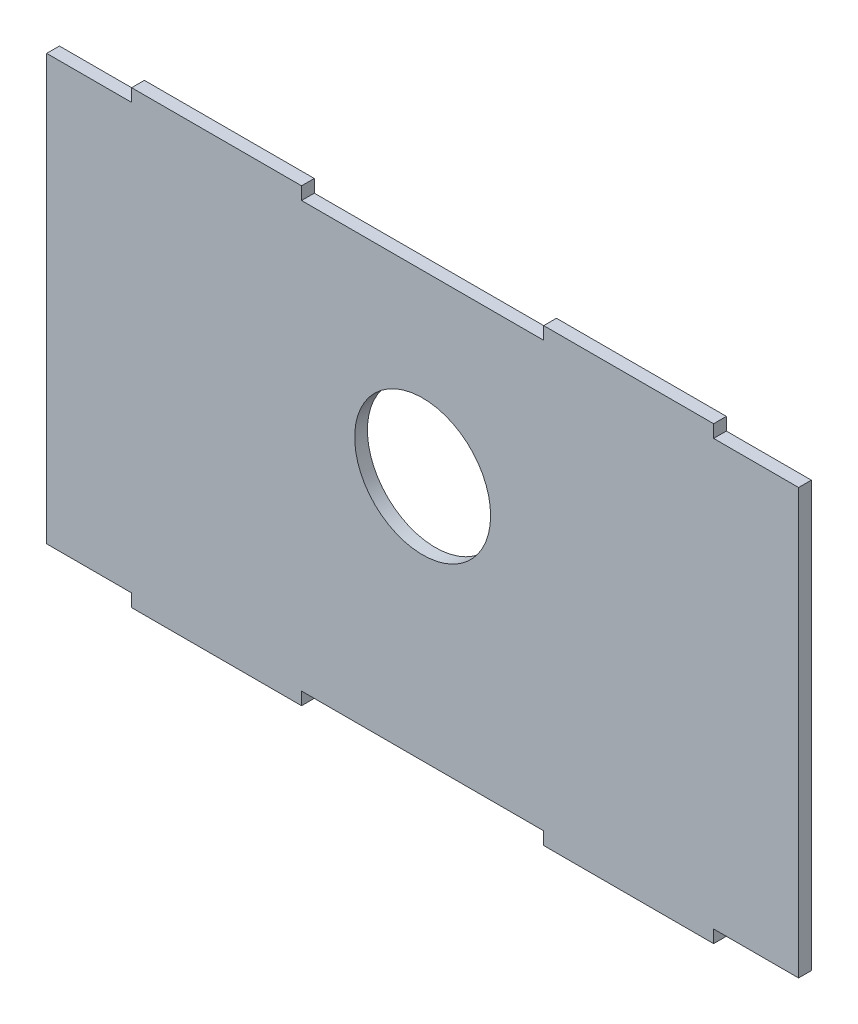
SolidWorks part; units mm, degrees
ref_plane "Front Plane" through (0, 0, 0) normal (0, 0, 1) x (1, 0, 0)
ref_plane "Top Plane" through (0, 0, 0) normal (0, 1, 0) x (1, 0, 0)
ref_plane "Right Plane" through (0, 0, 0) normal (1, 0, 0) x (0, 0, -1)
sketch "Sketch1" plane through (0, 0, 0) normal (0, 0, 1) x (1, 0, 0)
  line L0 (-28.5, 50) -> (28.5, 50)
  line L1 (-88.5, 50) -> (-68.5, 50)
  line L2 (-88.5, 50) -> (-88.5, -50)
  line L3 (-88.5, -50) -> (-68.5, -50)
  line L4 (88.5, 50) -> (88.5, -50)
  line L5 (-88.5, 50) -> (88.5, -50) construction
  line L6 (-88.5, -50) -> (88.5, 50) construction
  line L7 (68.5, 50) -> (88.5, 50)
  line L8 (-68.5, 50) -> (-68.5, 53)
  line L9 (-68.5, 53) -> (-28.5, 53)
  line L10 (-28.5, 50) -> (-28.5, 53)
  line L11 (-28.5, -50) -> (28.5, -50)
  line L12 (28.5, 50) -> (28.5, 53)
  line L13 (28.5, 53) -> (68.5, 53)
  line L14 (68.5, 50) -> (68.5, 53)
  line L15 (68.5, -50) -> (88.5, -50)
  line L16 (-68.5, -50) -> (-68.5, -53)
  line L17 (-68.5, -53) -> (-28.5, -53)
  line L18 (-28.5, -50) -> (-28.5, -53)
  line L20 (28.5, -50) -> (28.5, -53)
  line L21 (28.5, -53) -> (68.5, -53)
  line L22 (68.5, -50) -> (68.5, -53)
  circle A0 centre (0, 8) radius 16
  point P1 (0, 0)
  dimension "D3" = 42
  dimension "D4" = 32
  dimension "D1" = 100
  dimension "D2" = 177
  dimension "D5" = 40
  dimension "D6" = 40
  dimension "D7" = 40
  dimension "D8" = 40
  dimension "D9" = 20
  dimension "D10" = 20
  dimension "D11" = 20
  dimension "D12" = 20
  dimension "D13" = 3
  dimension "D14" = 3
  dimension "D15" = 3
  dimension "D16" = 3
extrude "Boss-Extrude1" add sketch "Sketch1" along normal mid plane 3
